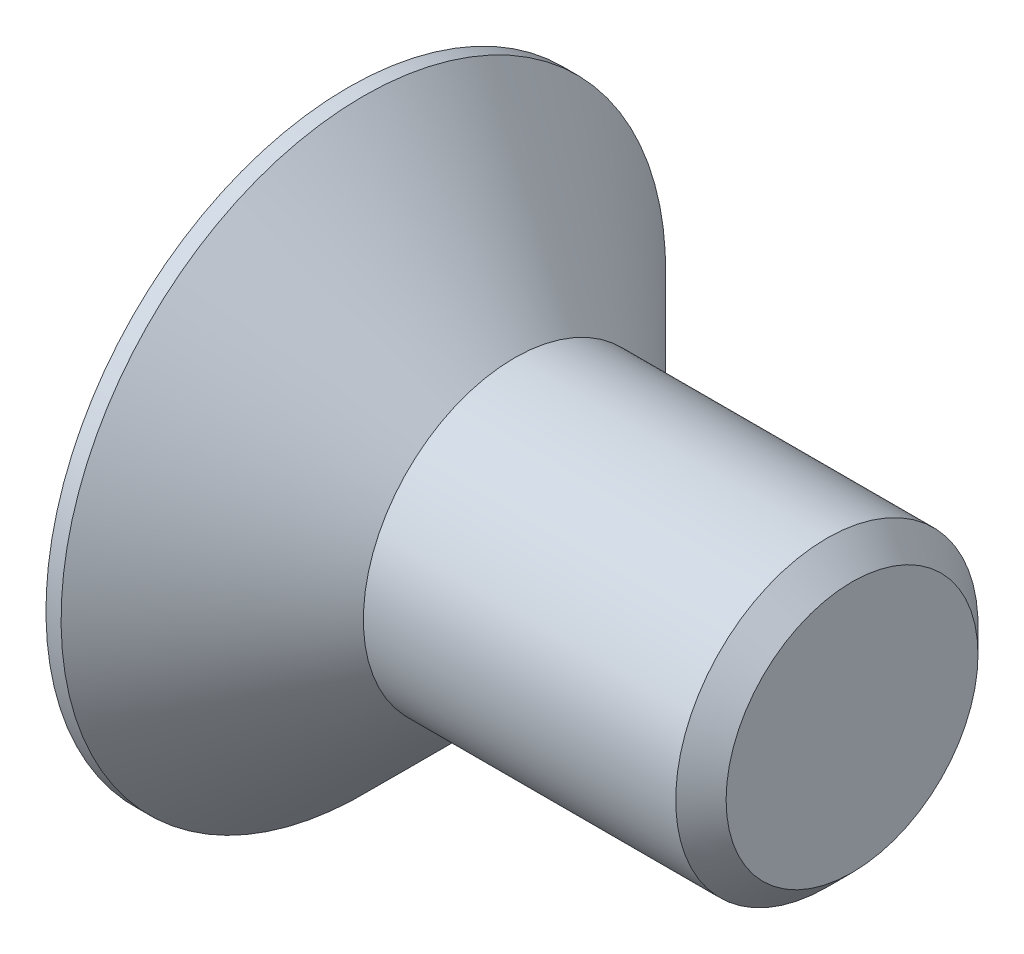
SolidWorks part; units mm, degrees
ref_plane "Plan de face" through (0, 0, 0) normal (0, 0, 1) x (1, 0, 0)
ref_plane "Plan de dessus" through (0, 0, 0) normal (0, 1, 0) x (1, 0, 0)
ref_plane "Plan de droite" through (0, 0, 0) normal (1, 0, 0) x (0, 0, -1)
sketch "Esquisse1" plane through (0, 0, 0) normal (0, 0, 1) x (1, 0, 0)
  line L0 (0, 0) -> (0, 6)
  line L1 (0, 6) -> (0.3, 6)
  line L2 (0.3, 6) -> (3.3, 3)
  line L3 (3.3, 3) -> (10, 3)
  line L4 (10, 3) -> (10, 0)
  line L5 (10, 0) -> (0, 0) construction
  line L6 (0, 0) -> (10, 0)
  dimension "D1" = 3.3
  dimension "D2" = 10
  dimension "D3" = 6
  dimension "D4" = 12
  dimension "D5" = 45
revolve "Révolution1" add sketch "Esquisse1" angle 360 about L5
chamfer "Chanfrein1" distance 0.5 angle 45 1 edges at (10, 3, 0)
sketch "Esquisse2" plane through (0, 0, 0) normal (-1, 0, 0) x (0, 0, 1)
  line L1 (0, 2.3094) -> (-2, 1.1547)
  line L2 (-2, 1.1547) -> (-2, -1.1547)
  line L3 (-2, -1.1547) -> (0, -2.3094)
  line L4 (0, -2.3094) -> (2, -1.1547)
  line L5 (2, -1.1547) -> (2, 1.1547)
  line L6 (2, 1.1547) -> (0, 2.3094)
  circle A0 centre (0, 0) radius 2 construction
  dimension "D1" = 4
extrude "Enlèv. mat.-Extru.1" cut sketch "Esquisse2" against normal blind 2.5
